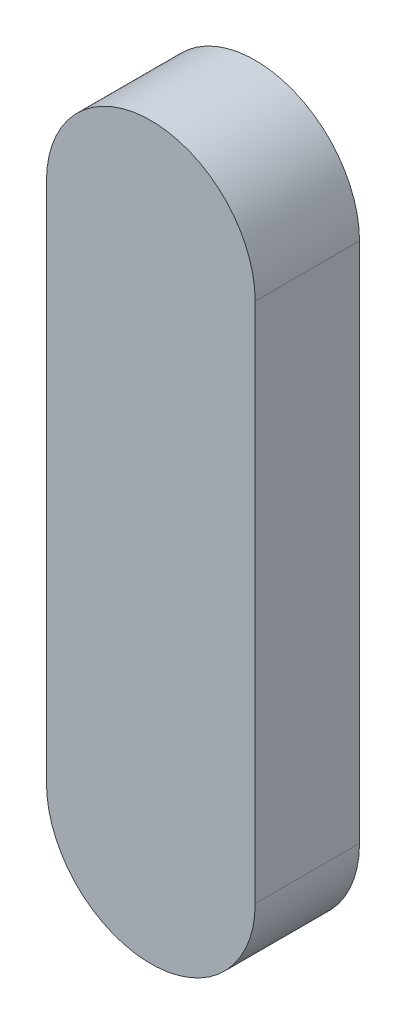
SolidWorks part; units mm, degrees
ref_plane "前视基准面" through (0, 0, 0) normal (0, 0, 1) x (1, 0, 0)
ref_plane "上视基准面" through (0, 0, 0) normal (0, 1, 0) x (1, 0, 0)
ref_plane "右视基准面" through (0, 0, 0) normal (1, 0, 0) x (0, 0, -1)
sketch "草图1" plane through (0, 0, 0) normal (0, 0, 1) x (1, 0, 0)
  line L0 (0, 0) -> (0, -25) construction
  line L1 (5, 0) -> (5, -25)
  line L2 (-5, 0) -> (-5, -25)
  arc A0 (5, 0) -> (-5, 0) centre (0, 0) ccw
  arc A1 (-5, -25) -> (5, -25) centre (0, -25) ccw
  point P3 (0, -12.5)
extrude "凸台-拉伸1" add sketch "草图1" along normal blind 5
